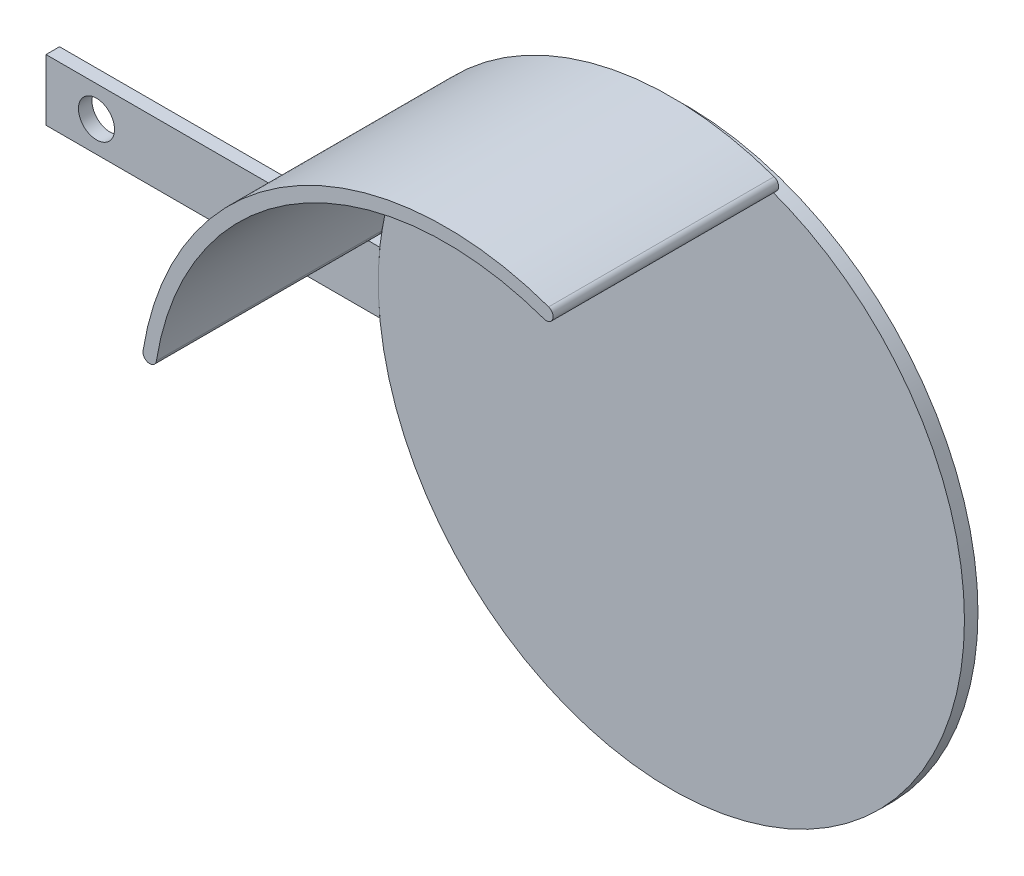
SolidWorks part; units mm, degrees
ref_plane "Plan de face" through (0, 0, 0) normal (0, 0, 1) x (1, 0, 0)
ref_plane "Plan de dessus" through (0, 0, 0) normal (0, 1, 0) x (1, 0, 0)
ref_plane "Plan de droite" through (0, 0, 0) normal (1, 0, 0) x (0, 0, -1)
sketch "Esquisse1" plane through (0, 0, 0) normal (0, 0, 1) x (1, 0, 0)
  circle A0 centre (0, 0) radius 65
  dimension "D1" = 130
extrude "Boss.-Extru.1" add sketch "Esquisse1" along normal blind 3
sketch "Esquisse2" plane through (0, 0, 3) normal (0, 0, 1) x (1, 0, 0)
  line L2 (0, 0) -> (-47.3168, -44.5659) construction
  line L4 (-61.9722, 1.8555) -> (-64.9709, 1.9452)
  line L5 (-1.8555, -61.9722) -> (-1.9452, -64.9709)
  arc A3 (-1.9452, -64.9709) -> (-64.9709, 1.9452) centre (0, 0) cw
  arc A4 (-1.8555, -61.9722) -> (-61.9722, 1.8555) centre (0, 0) cw
extrude "Boss.-Extru.2" [suppressed] add sketch "Esquisse2" along normal blind 60
sketch "Esquisse3" plane through (0, 0, 0) normal (0, 0, -1) x (-1, 0, 0)
  line L0 (0, 0) -> (113.8804, 0) construction
  line L1 (0, 0) -> (64.6439, 6.7944) construction
  line L2 (0, 0) -> (64.6439, -6.7944) construction
  line L3 (64.6439, 6.7944) -> (138.6725, 6.7944)
  line L4 (64.6439, -6.7944) -> (138.6725, -6.7944)
  line L5 (138.6725, -6.7944) -> (138.6725, 6.7944)
  arc A0 (64.6439, -6.7944) -> (64.6439, 6.7944) centre (0, 0) ccw
  circle A1 centre (0, 0) radius 65 construction
  dimension "D1" = 6
  dimension "D2" = 6
extrude "Boss.-Extru.3" add sketch "Esquisse3" against normal blind 3 separate body
sketch "Esquisse4" plane through (0, 0, 3) normal (0, 0, 1) x (1, 0, 0)
  circle A0 centre (-127.4771, 0) radius 4
extrude "Enlèv. mat.-Extru.1" cut sketch "Esquisse4" against normal blind 3
sketch "Esquisse5" plane through (0, 0, 3) normal (0, 0, 1) x (1, 0, 0)
  line L0 (39.6348, -66.7422) -> (-113.5458, 191.2029) construction
  arc A0 (21.784, 61.241) -> (-64.1978, 10.1808) centre (0, 0) ccw
  circle A1 centre (0, 0) radius 65 construction
  arc A2 (22.7894, 64.0675) -> (-67.1607, 10.6507) centre (0, 0) ccw
  arc A3 (21.784, 61.241) -> (22.7894, 64.0675) centre (22.2867, 62.6542) ccw
  arc A4 (-64.1978, 10.1808) -> (-67.1607, 10.6507) centre (-65.6792, 10.4157) cw
  dimension "D1" = 50
  dimension "D2" = 50
  dimension "D3" = 3
extrude "Boss.-Extru.4" add sketch "Esquisse5" along normal blind 50 separate body
